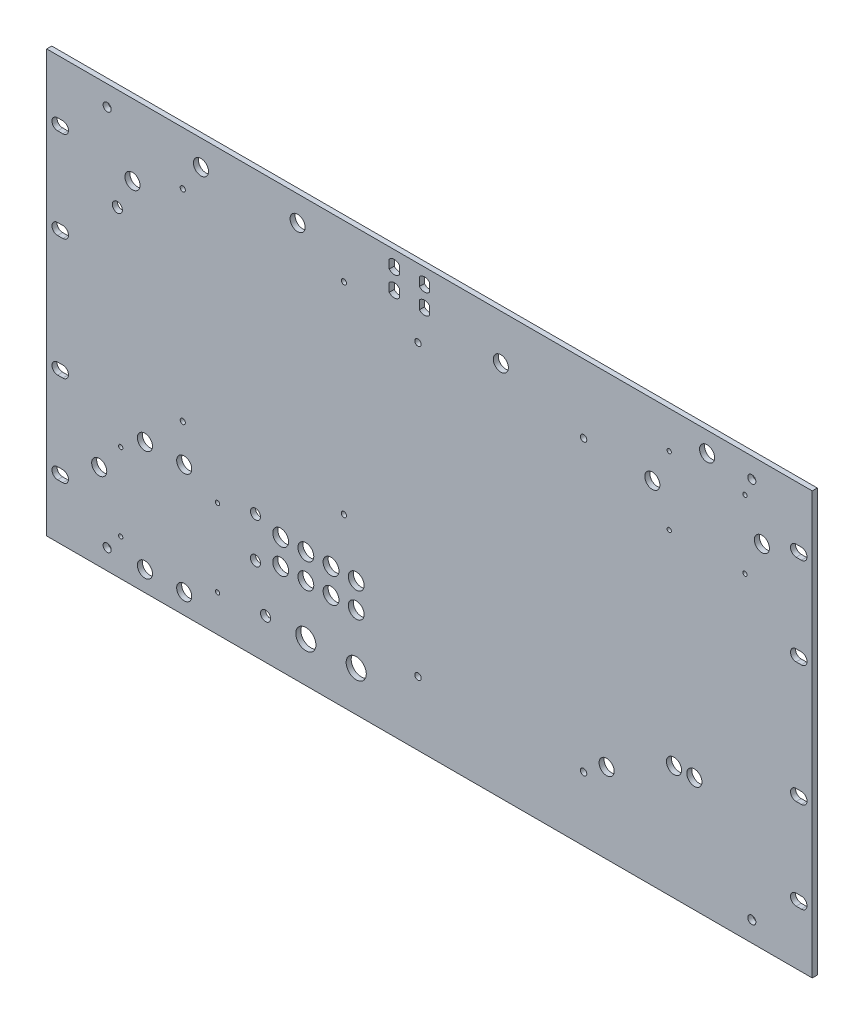
SolidWorks part; units mm, degrees
material "6061-T6 (SS)"
ref_plane "Front Plane" through (0, 0, 0) normal (0, 0, 1) x (1, 0, 0)
ref_plane "Top Plane" through (0, 0, 0) normal (0, 1, 0) x (1, 0, 0)
ref_plane "Right Plane" through (0, 0, 0) normal (1, 0, 0) x (0, 0, -1)
sketch "Sketch1" plane through (0, 0, 0) normal (0, 0, 1) x (1, 0, 0)
  line L1 (-241.3, 132.969) -> (241.3, 132.969)
  line L2 (-241.3, 132.969) -> (-241.3, -132.969)
  line L3 (-241.3, -132.969) -> (241.3, -132.969)
  line L4 (241.3, 132.969) -> (241.3, -132.969)
  line L5 (-241.3, 132.969) -> (241.3, -132.969) construction
  line L6 (-241.3, -132.969) -> (241.3, 132.969) construction
  point P0 (0, 0)
  dimension "D1" = 482.6
  dimension "D2" = 265.938
extrude "Boss-Extrude1" add sketch "Sketch1" along normal blind 3.175
sketch "Sketch2" plane through (0, 0, 3.175) normal (0, 0, 1) x (1, 0, 0)
  line L0 (-234.442, 95.25) -> (-231.14, 95.25) construction
  line L1 (-234.442, 98.806) -> (-231.14, 98.806)
  line L2 (-234.442, 91.694) -> (-231.14, 91.694)
  line L3 (-234.442, 38.1) -> (-231.14, 38.1) construction
  line L4 (-234.442, 41.656) -> (-231.14, 41.656)
  line L5 (-234.442, 34.544) -> (-231.14, 34.544)
  line L6 (-234.442, -38.1) -> (-231.14, -38.1) construction
  line L7 (-234.442, -34.544) -> (-231.14, -34.544)
  line L8 (-234.442, -41.656) -> (-231.14, -41.656)
  line L9 (-234.442, -95.25) -> (-231.14, -95.25) construction
  line L10 (-234.442, -91.694) -> (-231.14, -91.694)
  line L11 (-234.442, -98.806) -> (-231.14, -98.806)
  line L12 (-241.3, 132.969) -> (-241.3, -132.969) construction
  line L13 (-232.791, 38.1) -> (0, 0) construction
  line L14 (0, 0) -> (-232.791, -38.1) construction
  arc A0 (-234.442, 98.806) -> (-234.442, 91.694) centre (-234.442, 95.25) ccw
  arc A1 (-231.14, 91.694) -> (-231.14, 98.806) centre (-231.14, 95.25) ccw
  arc A2 (-234.442, 41.656) -> (-234.442, 34.544) centre (-234.442, 38.1) ccw
  arc A3 (-231.14, 34.544) -> (-231.14, 41.656) centre (-231.14, 38.1) ccw
  arc A4 (-234.442, -34.544) -> (-234.442, -41.656) centre (-234.442, -38.1) ccw
  arc A5 (-231.14, -41.656) -> (-231.14, -34.544) centre (-231.14, -38.1) ccw
  arc A6 (-234.442, -91.694) -> (-234.442, -98.806) centre (-234.442, -95.25) ccw
  arc A7 (-231.14, -98.806) -> (-231.14, -91.694) centre (-231.14, -95.25) ccw
  point P2 (-232.791, 95.25)
  point P8 (-232.791, 38.1)
  point P15 (-232.791, -38.1)
  point P22 (-232.791, -95.25)
  dimension "D1" = 10.414
  dimension "D3" = 13.716
  dimension "D2" = 7.112
  dimension "D4" = 76.2
  dimension "D5" = 57.15
  dimension "D6" = 57.15
extrude "Cut-Extrude1" cut sketch "Sketch2" against normal through all
mirror "Mirror1" about plane through (0, 0, 0) normal (1, 0, 0) of "Cut-Extrude1"
extrude "Cut-Extrude2" cut sketch "Sketch3" against normal through all
sketch "Sketch3" plane through (-181.0216, -243.6318, 3.175) normal (0, 0, 1) x (1, 0, 0)
  line L0 (181.0488, 369.7724) -> (181.0488, 364.3792)
  line L1 (174.6988, 369.7724) -> (174.6988, 364.3792)
  line L2 (161.9988, 369.7724) -> (161.9988, 364.3792)
  line L3 (155.6488, 369.7724) -> (155.6488, 364.3792)
  line L4 (161.9988, 357.0724) -> (161.9988, 351.6792)
  line L5 (155.6488, 357.0724) -> (155.6488, 351.6792)
  line L6 (174.6988, 357.0724) -> (174.6988, 351.6792)
  line L7 (181.0488, 357.0724) -> (181.0488, 351.6792)
  arc A0 (161.9988, 369.7724) -> (155.6488, 369.7724) centre (158.8238, 367.0758) ccw
  arc A1 (181.0488, 369.7724) -> (174.6988, 369.7724) centre (177.8738, 367.0758) ccw
  arc A2 (161.9988, 357.0724) -> (155.6488, 357.0724) centre (158.8238, 354.3758) ccw
  arc A3 (174.6988, 351.6792) -> (181.0488, 351.6792) centre (177.8738, 354.3758) ccw
  arc A4 (174.6988, 364.3792) -> (181.0488, 364.3792) centre (177.8738, 367.0758) ccw
  arc A5 (155.6488, 364.3792) -> (161.9988, 364.3792) centre (158.8238, 367.0758) ccw
  arc A6 (155.6488, 351.6792) -> (161.9988, 351.6792) centre (158.8238, 354.3758) ccw
  arc A7 (181.0488, 357.0724) -> (174.6988, 357.0724) centre (177.8738, 354.3758) ccw
extrude "Cut-Extrude3" cut sketch "Sketch4" against normal through all
sketch "Sketch4" plane through (-181.0216, -243.6318, 3.175) normal (0, 0, 1) x (1, 0, 0)
  line L0 (91.8874, 339.1858) -> (97.8874, 360.6514) construction
  line L1 (97.8874, 360.6514) -> (103.8874, 339.1858) construction
  line L3 (35.4679, 341.1897) -> (36.9468, 360.6514) construction
  line L4 (36.9468, 360.6514) -> (38.4257, 341.1897) construction
  circle A0 centre (97.8874, 360.6514) radius 4.7625
  circle A1 centre (36.9468, 360.6514) radius 4.7625
extrude "Cut-Extrude4" cut sketch "Sketch5" against normal through all
sketch "Sketch5" plane through (-181.0216, -243.6318, 3.175) normal (0, 0, 1) x (1, 0, 0)
  line L0 (224.8332, 330.1744) -> (225.9932, 348.0258) construction
  line L1 (225.9932, 348.0258) -> (227.1532, 330.1744) construction
  line L3 (269.8488, 161.8083) -> (292.6935, 161.0583) construction
  line L4 (292.6935, 161.0583) -> (269.8488, 160.3083) construction
  circle A0 centre (225.9932, 348.0258) radius 4.7625
  circle A1 centre (292.6935, 161.0583) radius 4.7625
hole_wizard "#4 Clearance Hole1" positions "Sketch6" profile "Sketch7" hole size "#4" standard "ANSI Inch" end condition through all
sketch "Sketch6" plane through (-181.0216, -243.6318, 0) normal (0, 0, -1) x (-1, 0, 0)
  point P0 (-127.0974, 343.1109)
  point P2 (-25.4974, 343.1109)
  point P4 (-25.4974, 216.1109)
  point P6 (-127.0974, 216.1109)
sketch "Sketch7" plane through (-53.9242, 99.4791, 0) normal (1, 0, 0) x (0, 1, 0)
  line L0 (0, 0) -> (0, 3.175)
  line L1 (0, 3.175) -> (1.6319, 3.175)
  line L2 (1.6319, 3.175) -> (1.6319, 0)
  line L3 (1.6319, 0) -> (0, 0)
  line L4 (0, -6.35) -> (0, 107.95) construction
  dimension "Thru Hole Dia." = 3.2639
  dimension "Thru Hole Depth" = 3.175
extrude "Cut-Extrude5" cut sketch "Sketch8" against normal through all
sketch "Sketch8" plane through (-181.0216, -243.6318, 3.175) normal (0, 0, 1) x (1, 0, 0)
  line L0 (71.3357, 188.4582) -> (87.2107, 183.6957) construction
  line L1 (87.2107, 167.8207) -> (71.3357, 163.0582) construction
  circle A0 centre (87.2107, 183.6957) radius 5
  circle A1 centre (103.0857, 183.6957) radius 5
  circle A2 centre (118.9607, 183.6957) radius 5
  circle A3 centre (134.8357, 183.6957) radius 5
  circle A4 centre (134.8357, 167.8207) radius 5
  circle A5 centre (118.9607, 167.8207) radius 5
  circle A6 centre (103.0857, 167.8207) radius 5
  circle A7 centre (87.2107, 167.8207) radius 5
  circle A8 centre (71.3357, 188.4582) radius 3.175
  circle A9 centre (71.3357, 163.0582) radius 3.175
  circle A10 centre (103.0857, 136.0707) radius 6.35
  circle A11 centre (134.8357, 136.0707) radius 6.35
  circle A12 centre (77.6857, 136.0707) radius 3.175
extrude "Cut-Extrude6" cut sketch "Sketch9" against normal through all
sketch "Sketch9" plane through (-181.0216, -243.6318, 3.175) normal (0, 0, 1) x (1, 0, 0)
  line L0 (23.3175, 138.8488) -> (26.3932, 123.3628) construction
  line L1 (26.3932, 123.3628) -> (29.4975, 138.8431) construction
  line L2 (-1.4593, 136.182) -> (1.6307, 123.3628) construction
  line L3 (1.6307, 123.3628) -> (4.7207, 136.182) construction
  line L6 (-1.4593, 180.165) -> (1.6307, 192.9588) construction
  line L7 (1.6307, 192.9588) -> (4.7207, 180.165) construction
  line L10 (-11.1401, 167.9509) -> (-27.1853, 164.8609) construction
  line L11 (-27.1853, 164.8609) -> (-11.1401, 161.7709) construction
  circle A0 centre (26.3932, 192.9588) radius 4.7625
  circle A1 centre (1.6307, 192.9588) radius 4.7625
  circle A2 centre (1.6307, 123.3628) radius 4.7625
  circle A3 centre (26.3932, 123.3628) radius 4.7625
  circle A4 centre (-27.1853, 164.8609) radius 4.7625
extrude "Cut-Extrude7" cut sketch "Sketch10" against normal through all
sketch "Sketch10" plane through (-181.0216, -243.6318, 3.175) normal (0, 0, 1) x (1, 0, 0)
  line L1 (7.8443, 335.3221) -> (-6.229, 331.4721) construction
  line L2 (-6.229, 331.4721) -> (7.8443, 327.6221) construction
  circle A0 centre (-15.754, 312.4221) radius 3.175
  circle A1 centre (-6.229, 331.4721) radius 4.7625
hole_wizard "#6-32 Tapped Hole" positions "Sketch11" profile "Sketch12" tap size "#6-32" standard "ANSI Inch" end condition through all
sketch "Sketch11" plane through (-181.0216, -243.6318, 3.175) normal (0, 0, 1) x (1, 0, 0)
  point P0 (-13.6344, 182.5829)
  point P2 (47.4018, 182.5829)
  point P4 (47.4018, 133.7387)
  point P6 (-13.6344, 133.7387)
  point P25 (332.1516, 353.2328)
  point P27 (379.9036, 353.2328)
  point P29 (379.9036, 310.1798)
  point P31 (332.154, 310.1798)
sketch "Sketch12" plane through (-194.656, -61.0489, 3.175) normal (1, 0, 0) x (0, -1, 0)
  line L0 (0, 0) -> (0, 3.175)
  line L1 (0, 3.175) -> (1.3525, 3.175)
  line L2 (1.3525, 3.175) -> (1.3525, 0)
  line L3 (1.3525, 0) -> (0, 0)
  line L4 (0, -6.35) -> (0, 107.95) construction
  dimension "Thread Major Dia." = 2.7051
  dimension "Thru Tap Drill Depth" = 3.175
hole_wizard "#10-32 Tapped Hole1" positions "Sketch13" profile "Sketch14" tap size "#10-32" standard "ANSI Inch" end condition through all
sketch "Sketch13" plane through (-181.0216, -243.6318, 3.175) normal (0, 0, 1) x (1, 0, 0)
  point P0 (278.168, 333.2983)
  point P2 (173.774, 333.2983)
  point P4 (173.774, 151.0279)
  point P6 (278.168, 151.0279)
sketch "Sketch14" plane through (97.1464, 89.6665, 3.175) normal (1, 0, 0) x (0, -1, 0)
  line L0 (0, 0) -> (0, 3.175)
  line L1 (0, 3.175) -> (2.0193, 3.175)
  line L2 (2.0193, 3.175) -> (2.0193, 0)
  line L3 (2.0193, 0) -> (0, 0)
  line L4 (0, -6.35) -> (0, 107.95) construction
  dimension "Thru Tap Drill Dia." = 4.0386
  dimension "Thru Tap Drill Depth" = 3.175
cosmetic thread "Hole Thread1"
cosmetic thread "Hole Thread2"
cosmetic thread "Hole Thread3"
cosmetic thread "Hole Thread4"
extrude "Cut-Extrude8" cut sketch "Sketch15" against normal through all
sketch "Sketch15" plane through (-181.0216, -243.6318, 3.175) normal (0, 0, 1) x (1, 0, 0)
  line L4 (334.3028, 334.8468) -> (321.4836, 331.7568) construction
  line L5 (321.4836, 331.7568) -> (334.3028, 328.6668) construction
  line L6 (352.9429, 351.1011) -> (356.0329, 363.9008) construction
  line L7 (356.0329, 363.9008) -> (359.1229, 351.1011) construction
  line L8 (377.7723, 334.8493) -> (390.5716, 331.7593) construction
  line L9 (390.5716, 331.7593) -> (377.7723, 328.6693) construction
  circle A0 centre (321.4836, 331.7568) radius 4.7625
  circle A1 centre (356.0329, 363.9008) radius 4.7625
  circle A2 centre (390.5716, 331.7593) radius 4.7625
extrude "Cut-Extrude9" cut sketch "Sketch16" against normal through all
sketch "Sketch16" plane through (-181.0216, -243.6318, 3.175) normal (0, 0, 1) x (1, 0, 0)
  circle A0 centre (335.1614, 182.8948) radius 4.7625
  circle A1 centre (348.0233, 182.8948) radius 4.7625
hole_wizard "#10 Clearance Hole1" positions "Sketch17" profile "Sketch18" hole size "#10" standard "ANSI Inch" end condition through all
sketch "Sketch17" plane through (-181.0216, -243.6318, 3.175) normal (0, 0, 1) x (1, 0, 0)
  point P0 (-22.1784, 363.9008)
  point P2 (384.2216, 363.9008)
  point P4 (384.2216, 123.3628)
  point P6 (-22.1784, 123.3628)
sketch "Sketch18" plane through (-203.2, 120.269, 3.175) normal (1, 0, 0) x (0, -1, 0)
  line L0 (0, 0) -> (0, 3.175)
  line L1 (0, 3.175) -> (2.5527, 3.175)
  line L2 (2.5527, 3.175) -> (2.5527, 0)
  line L3 (2.5527, 0) -> (0, 0)
  line L4 (0, -6.35) -> (0, 107.95) construction
  dimension "Thru Hole Dia." = 5.1054
  dimension "Thru Hole Depth" = 3.175
